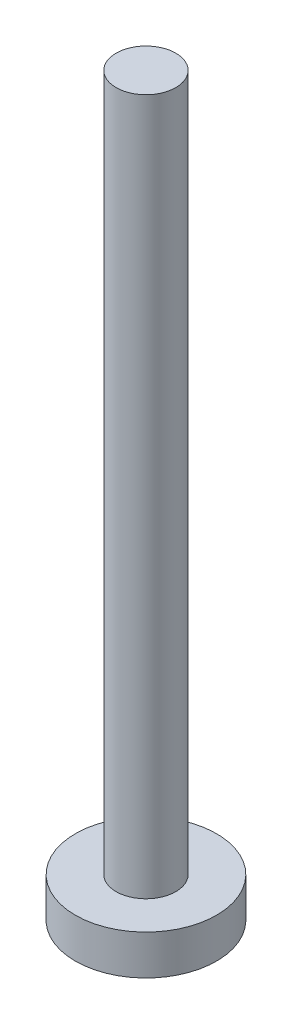
SolidWorks part; units mm, degrees
ref_plane "前视基准面" through (0, 0, 0) normal (0, 0, 1) x (1, 0, 0)
ref_plane "上视基准面" through (0, 0, 0) normal (0, 1, 0) x (1, 0, 0)
ref_plane "右视基准面" through (0, 0, 0) normal (1, 0, 0) x (0, 0, -1)
sketch "草图1" plane through (0, 0, 0) normal (0, 1, 0) x (1, 0, 0)
  circle A0 centre (0, 0) radius 3.55
  dimension "D1" = 7.1
extrude "凸台-拉伸1" add sketch "草图1" along normal blind 2
sketch "草图2" plane through (0, 2, 0) normal (0, 1, 0) x (1, 0, 0)
  circle A0 centre (0, 0) radius 1.5
  dimension "D1" = 3
extrude "凸台-拉伸2" add sketch "草图2" along normal blind 35
